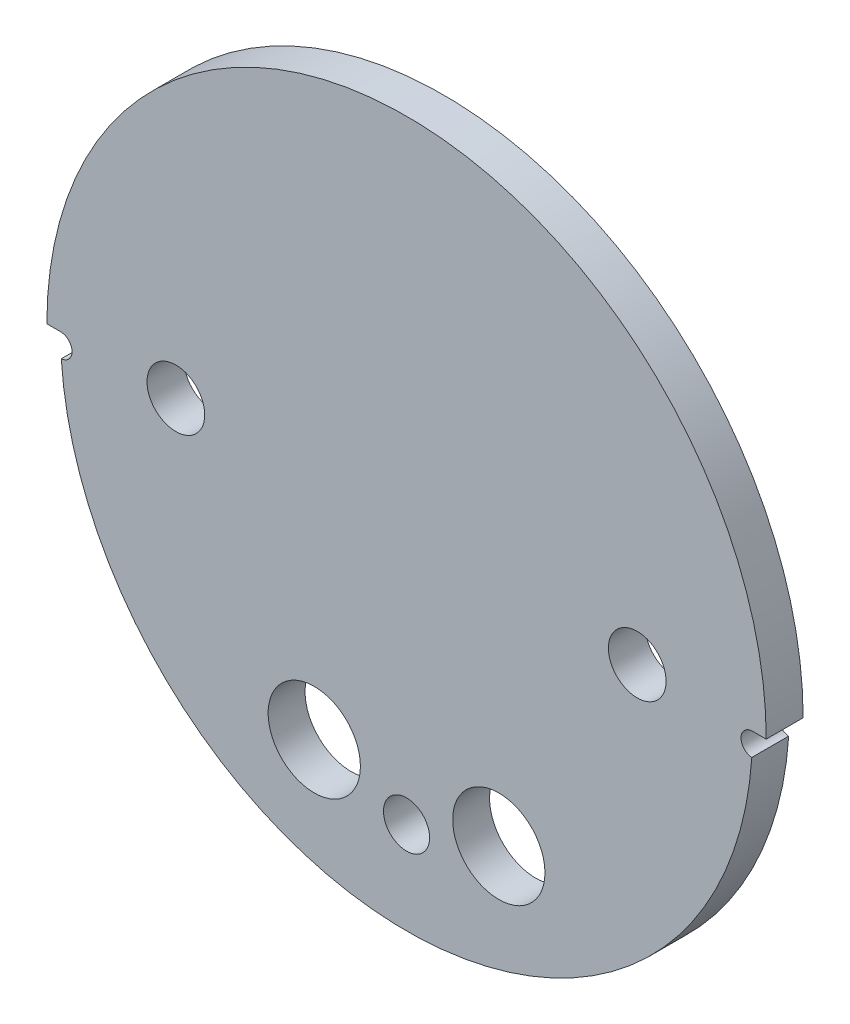
SolidWorks part; units mm, degrees
ref_plane "Front Plane" through (0, 0, 0) normal (0, 0, 1) x (1, 0, 0)
ref_plane "Top Plane" through (0, 0, 0) normal (0, 1, 0) x (1, 0, 0)
ref_plane "Right Plane" through (0, 0, 0) normal (1, 0, 0) x (0, 0, -1)
sketch "Sketch1" plane through (0, 0, 0) normal (0, 0, 1) x (1, 0, 0)
  circle A0 centre (0, 0) radius 49.5046
  dimension "D1" = 99.0092
extrude "Boss-Extrude1" add sketch "Sketch1" along normal blind 5.08
sketch "Sketch2" plane through (0, 0, 5.08) normal (0, 0, 1) x (1, 0, 0)
  circle A0 centre (0, 0) radius 47.625
  dimension "D1" = 95.25
extrude "Boss-Extrude2" add sketch "Sketch2" along normal blind 3.175
sketch "Sketch3" plane through (0, 0, 8.255) normal (0, 0, 1) x (1, 0, 0)
  line L0 (-7.9375, -31.1668) -> (7.9375, -31.1668) construction
  circle A0 centre (-31.75, 0) radius 3.9688
  circle A1 centre (31.75, 0) radius 3.9687
  circle A2 centre (-12.7, -31.1668) radius 6.35
  circle A3 centre (-12.7, -31.1668) radius 13.97 construction
  circle A4 centre (-12.7, -31.1668) radius 4.7625 construction
  circle A5 centre (0, 0) radius 47.625 construction
  circle A6 centre (12.7, -31.1668) radius 6.35
  circle A7 centre (12.7, -31.1668) radius 13.97 construction
  circle A8 centre (-12.7, -31.1668) radius 12.7 construction
  circle A9 centre (12.7, -31.1668) radius 12.7 construction
  circle A10 centre (12.7, -31.1668) radius 4.7625 construction
  dimension "D1" = 7.9375
  dimension "D2" = 7.9375
  dimension "D5" = 12.7
  dimension "D6" = 27.94
  dimension "D7" = 12.7
  dimension "D8" = 27.94
  dimension "D9" = 25.4
  dimension "D10" = 25.4
  dimension "D11" = 9.525
  dimension "D12" = 9.525
  dimension "D3" = 63.5
  dimension "D4" = 31.75
extrude "Cut-Extrude1" cut sketch "Sketch3" against normal through all
sketch "Sketch4" plane through (0, 0, 5.08) normal (0, 0, 1) x (1, 0, 0)
  line L0 (-50.165, 0) -> (-47.625, 0)
  line L1 (47.625, 0) -> (50.165, 0)
  arc A0 (-50.165, 0) -> (50.165, 0) centre (0, 0) ccw
  arc A1 (-47.625, 0) -> (47.625, 0) centre (0, 0) ccw
extrude "Cut-Extrude2" cut sketch "Sketch4" against normal through all
sketch "Sketch5" plane through (0, 0, 8.255) normal (0, 0, 1) x (1, 0, 0)
  circle A0 centre (0, 0) radius 54.4123
extrude "Cut-Extrude3" cut sketch "Sketch5" against normal blind 3.175
sketch "Sketch6" plane through (0, 0, 0) normal (0, 0, -1) x (-1, 0, 0)
  circle A0 centre (-47.625, -1.5875) radius 1.5875
  circle A2 centre (47.625, -1.5875) radius 1.5875
  dimension "D1" = 3.175
  dimension "D2" = 3.175
extrude "Cut-Extrude4" cut sketch "Sketch6" against normal through all
sketch "Sketch7" plane through (0, 0, 5.08) normal (0, 0, 1) x (1, 0, 0)
  circle A0 centre (0, -34.925) radius 3.175
  arc A1 (-47.5193, -3.1715) -> (47.5193, -3.1715) centre (0, 0) ccw construction
  point P2 (0, -47.625)
  dimension "D1" = 6.35
  dimension "D2" = 12.7
extrude "Cut-Extrude5" cut sketch "Sketch7" against normal through all
